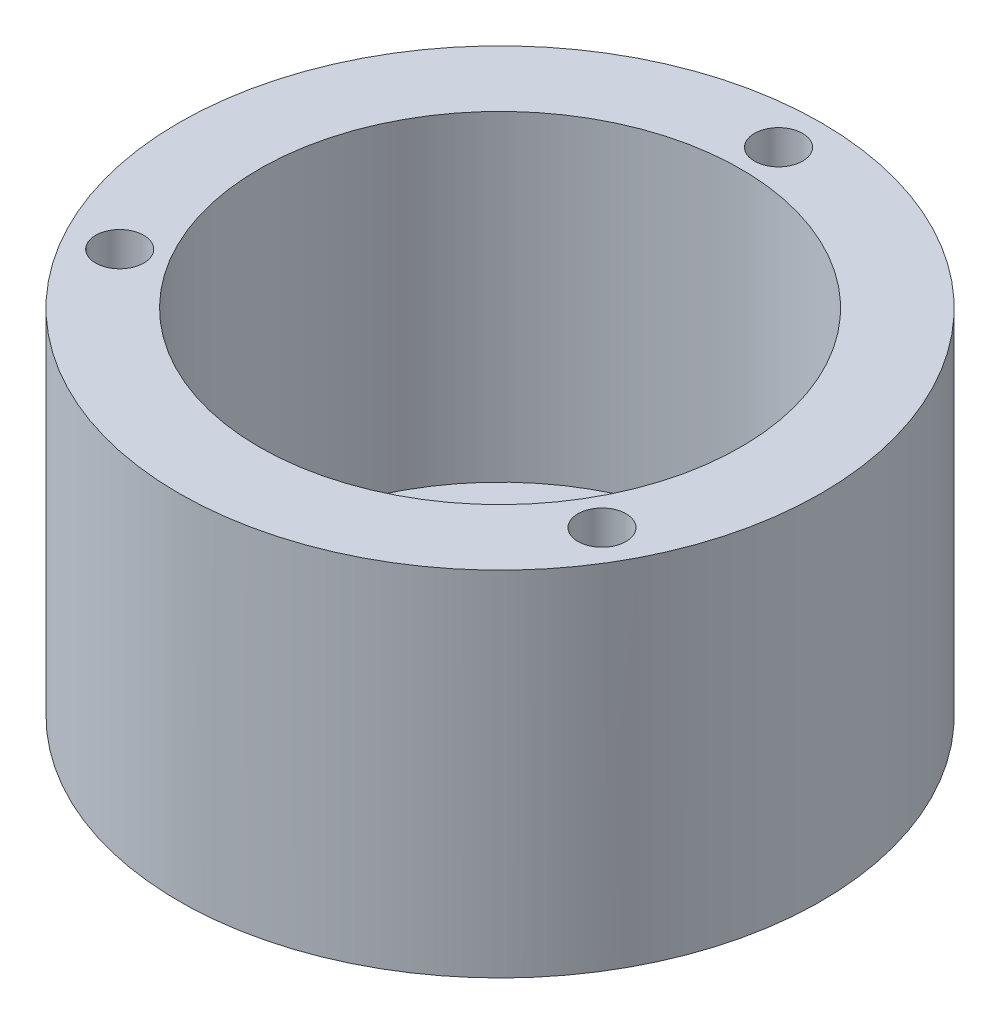
SolidWorks part; units mm, degrees
material "1060 Alloy"
ref_plane "Front Plane" through (0, 0, 0) normal (0, 0, 1) x (1, 0, 0)
ref_plane "Top Plane" through (0, 0, 0) normal (0, 1, 0) x (1, 0, 0)
ref_plane "Right Plane" through (0, 0, 0) normal (1, 0, 0) x (0, 0, -1)
sketch "Sketch1" plane through (0, 0, 0) normal (0, 1, 0) x (1, 0, 0)
  circle A0 centre (0, 0) radius 20
  circle A1 centre (0, 0) radius 15
extrude "Boss-Extrude1" add sketch "Sketch1" along normal blind 20
sketch "Sketch2" plane through (0, 0, 0) normal (0, -1, 0) x (1, 0, 0)
  circle A0 centre (0, 0) radius 20
  circle A1 centre (0, 0) radius 3
  circle A2 centre (6, 7.4634) radius 2
  circle A3 centre (7.4634, -6) radius 2
  circle A4 centre (-6, -7.4634) radius 2
  circle A5 centre (-7.4634, 6) radius 2
  point P15 (0, 0)
  dimension "D1" = 6
  dimension "D2" = 4
extrude "Boss-Extrude2" add sketch "Sketch2" along normal blind 2
sketch "Sketch3" plane through (0, 20, 0) normal (0, 1, 0) x (1, 0, 0)
  circle A0 centre (0, 17.3437) radius 1.5
  circle A1 centre (15.0201, -8.6719) radius 1.5
  circle A2 centre (-15.0201, -8.6719) radius 1.5
  point P9 (0, 0)
  dimension "D1" = 3
extrude "Cut-Extrude1" cut sketch "Sketch3" against normal blind 4
